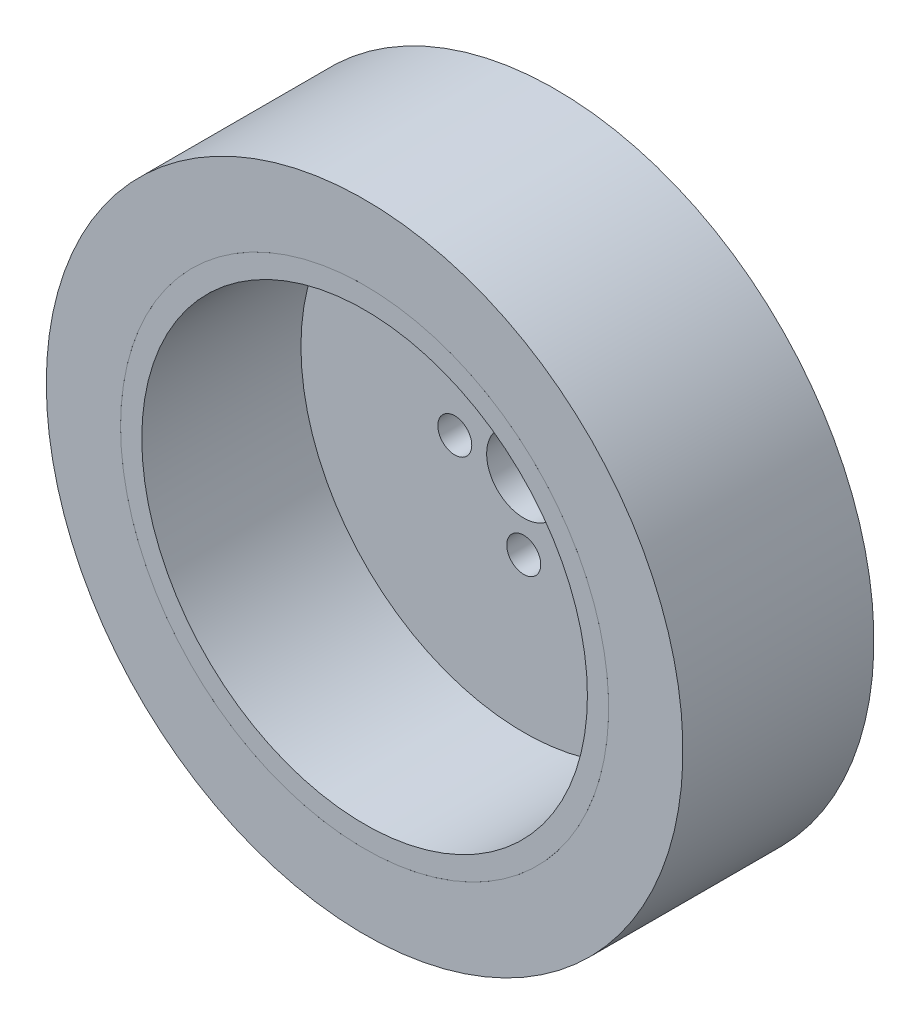
SolidWorks part; units mm, degrees
material "6061 合金"
ref_plane "前视基准面" through (0, 0, 0) normal (0, 0, 1) x (1, 0, 0)
ref_plane "上视基准面" through (0, 0, 0) normal (0, 1, 0) x (1, 0, 0)
ref_plane "右视基准面" through (0, 0, 0) normal (1, 0, 0) x (0, 0, -1)
sketch "草图1" plane through (0, 0, 0) normal (0, 1, 0) x (1, 0, 0)
  line L0 (0, 0) -> (0, -15.6625) construction
  line L1 (-3.5, 0) -> (-23, 0)
  line L2 (-23, 0) -> (-23, -18)
  line L3 (-23, -18) -> (-21, -18)
  line L4 (-21, -18) -> (-21, -3)
  line L5 (-21, -3) -> (-3.5, -3)
  line L6 (-3.5, -3) -> (-3.5, 0)
  dimension "D1" = 7
  dimension "D2" = 42
  dimension "D3" = 3
  dimension "D4" = 2
  dimension "D5" = 18
revolve "旋转1" add sketch "草图1" angle 360 about L0
sketch "草图2" plane through (0, 0, 0) normal (0, 0, -1) x (-1, 0, 0)
  circle A0 centre (0, 0) radius 6.5 construction
  circle A1 centre (6.5, 0) radius 1.6
  circle A2 centre (0, -6.5) radius 1.6
  circle A3 centre (-6.5, 0) radius 1.6
  circle A4 centre (0, 6.5) radius 1.6
  point P14 (0, 0)
  dimension "D1" = 13
  dimension "D2" = 3.2
  dimension "D3" = 4
extrude "切除-拉伸1" cut sketch "草图2" against normal blind 10
sketch "草图3" plane through (0, 0, 0) normal (0, 1, 0) x (1, 0, 0)
  line L0 (-23.001, 0) -> (-23.001, -18)
  line L1 (-23.001, -18) -> (-30, -18)
  line L2 (-30, -18) -> (-30, 0)
  line L3 (-30, 0) -> (-23.001, 0)
  line L5 (-23, -18) -> (23, -18) construction
  line L6 (0, 0) -> (0, -18) construction
  line L7 (1.6, 0) -> (-1.6, 0) construction
  line L8 (-27.5885, -9) -> (0, -9) construction
  line L9 (23, 0) -> (-23, 0) construction
  line L10 (-23, 0) -> (-23, -18) construction
  arc A0 (-30, -18) -> (-30, 0) centre (-45.5885, -9) ccw construction
  dimension "D4" = 18
  dimension "D1" = 0.001
  dimension "D2" = 60
revolve "旋转2" add sketch "草图3" angle 360 about L6
